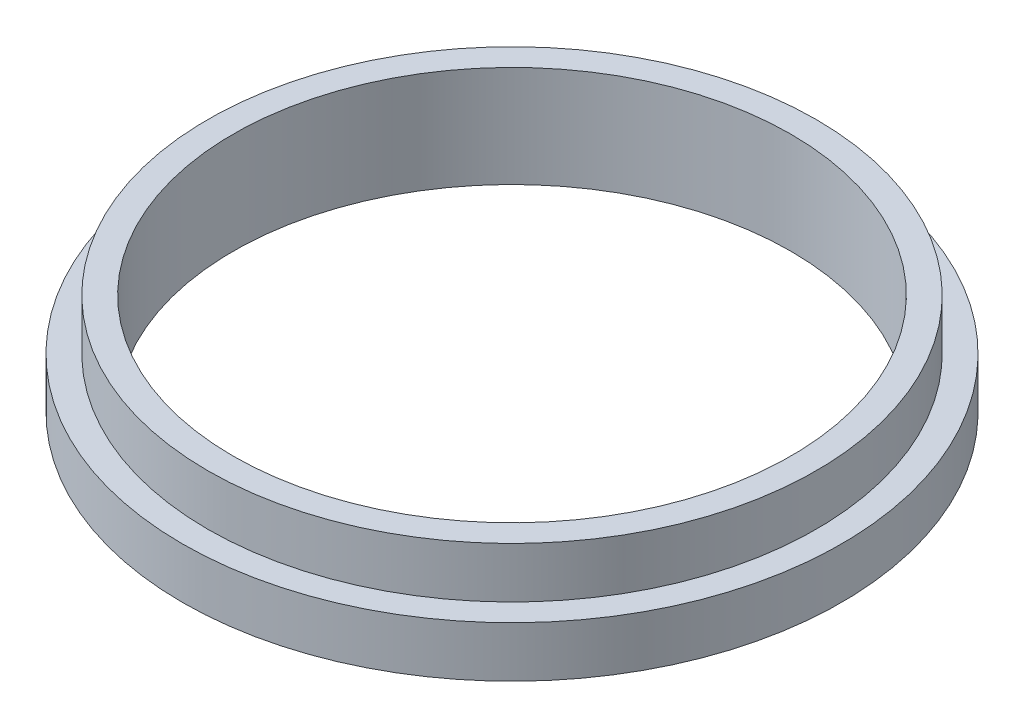
SolidWorks part; units mm, degrees
ref_plane "Alzado" through (0, 0, 0) normal (0, 0, 1) x (1, 0, 0)
ref_plane "Planta" through (0, 0, 0) normal (0, 1, 0) x (1, 0, 0)
ref_plane "Vista lateral" through (0, 0, 0) normal (1, 0, 0) x (0, 0, -1)
sketch "Croquis2" plane through (0, 0, 0) normal (0, 1, 0) x (1, 0, 0)
  circle A0 centre (0, 0) radius 55
  circle A1 centre (0, 0) radius 65
  dimension "D1" = 110
  dimension "D2" = 130
extrude "Saliente-Extruir1" add sketch "Croquis2" along normal blind 10
sketch "Croquis3" plane through (0, 10, 0) normal (0, 1, 0) x (1, 0, 0)
  circle A0 centre (0, 0) radius 55 construction
  circle A1 centre (0, 0) radius 55
  circle A2 centre (0, 0) radius 60
  dimension "D1" = 120
extrude "Saliente-Extruir2" add sketch "Croquis3" along normal blind 10
